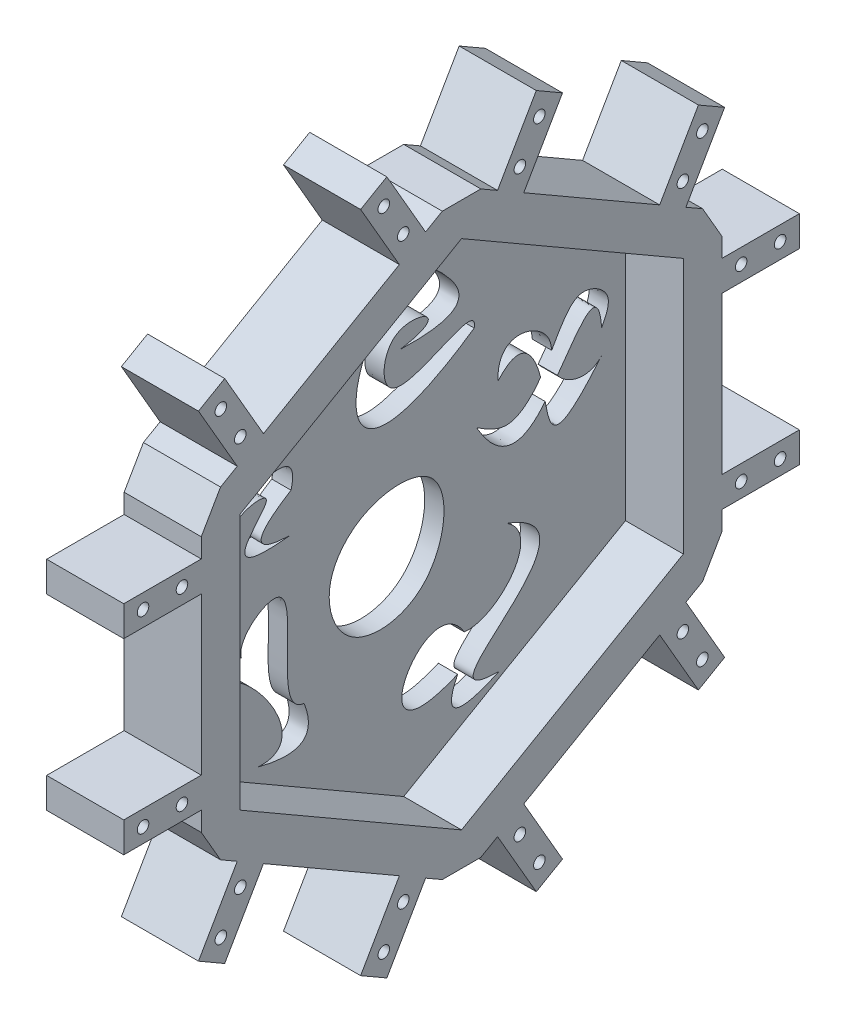
SolidWorks part; units mm, degrees
ref_plane "前视基准面" through (0, 0, 0) normal (0, 0, 1) x (1, 0, 0)
ref_plane "上视基准面" through (0, 0, 0) normal (0, 1, 0) x (1, 0, 0)
ref_plane "右视基准面" through (0, 0, 0) normal (1, 0, 0) x (0, 0, -1)
other "Configuration Table"
sketch "草图4" plane through (0, 0, 0) normal (1, 0, 0) x (0, 0, -1)
  line L0 (-57.5041, 33.2) -> (-57.5041, -23.2136)
  line L1 (-67.5041, -20.35) -> (-87.6041, -20.35)
  line L2 (-67.5041, 20.35) -> (-87.6041, 20.35)
  line L3 (-87.6041, 20.35) -> (-87.6041, 28.2)
  line L4 (-87.6041, 28.2) -> (-71.9735, 28.2)
  line L5 (-87.6041, -20.35) -> (-87.6041, -28.2)
  line L6 (-87.6041, -28.2) -> (-71.9735, -28.2)
  line L7 (-67.5041, 20.35) -> (-67.5041, -20.35)
  line L8 (-71.9735, 28.2) -> (-67.5041, 28.2)
  line L9 (-71.9735, -28.2) -> (-67.5041, -28.2)
  line L10 (-67.5041, 28.2) -> (-67.5041, 33.2)
  line L11 (0, 66.4) -> (-57.5041, 33.2) construction
  line L12 (-57.5041, 33.2) -> (-57.5041, -33.2) construction
  line L13 (-57.5041, -33.2) -> (0, -66.4) construction
  line L14 (0, -66.4) -> (57.5041, -33.2) construction
  line L15 (57.5041, -33.2) -> (57.5041, 33.2) construction
  line L16 (57.5041, 33.2) -> (0, 66.4) construction
  line L19 (-67.5041, -28.2) -> (-67.5041, -33.2)
  line L21 (-57.5041, -33.2) -> (-57.5041, -23.2136)
  line L22 (0, 66.4) -> (-48.8556, 38.1932)
  line L23 (-57.5041, 33.2) -> (-48.8556, 38.1932)
  line L25 (-58.174, 44.3603) -> (-62.5041, 41.8603)
  line L26 (-60.4087, 48.2309) -> (-58.174, 44.3603)
  line L27 (-68.224, 61.7674) -> (-60.4087, 48.2309)
  line L28 (-61.4257, 65.6924) -> (-68.224, 61.7674)
  line L29 (-51.3757, 48.2853) -> (-61.4257, 65.6924)
  line L30 (-16.1284, 68.6353) -> (-51.3757, 48.2853)
  line L31 (-16.1284, 68.6353) -> (-26.1784, 86.0424)
  line L32 (-26.1784, 86.0424) -> (-19.3801, 89.9674)
  line L33 (-19.3801, 89.9674) -> (-11.5648, 76.4309)
  line L34 (-11.5648, 76.4309) -> (-9.3301, 72.5603)
  line L35 (-9.3301, 72.5603) -> (-5, 75.0603)
  line L37 (57.5041, 33.2) -> (8.6484, 61.4068)
  line L38 (0, 66.4) -> (8.6484, 61.4068)
  line L40 (9.3301, 72.5603) -> (5, 75.0603)
  line L41 (11.5648, 76.4309) -> (9.3301, 72.5603)
  line L42 (19.3801, 89.9674) -> (11.5648, 76.4309)
  line L43 (26.1784, 86.0424) -> (19.3801, 89.9674)
  line L44 (16.1284, 68.6353) -> (26.1784, 86.0424)
  line L45 (51.3757, 48.2853) -> (16.1284, 68.6353)
  line L46 (51.3757, 48.2853) -> (61.4257, 65.6924)
  line L47 (61.4257, 65.6924) -> (68.224, 61.7674)
  line L48 (68.224, 61.7674) -> (60.4087, 48.2309)
  line L49 (60.4087, 48.2309) -> (58.174, 44.3603)
  line L50 (58.174, 44.3603) -> (62.5041, 41.8603)
  line L52 (57.5041, -33.2) -> (57.5041, 23.2136)
  line L53 (57.5041, 33.2) -> (57.5041, 23.2136)
  line L55 (67.5041, 28.2) -> (67.5041, 33.2)
  line L56 (71.9735, 28.2) -> (67.5041, 28.2)
  line L57 (87.6041, 28.2) -> (71.9735, 28.2)
  line L58 (87.6041, 20.35) -> (87.6041, 28.2)
  line L59 (67.5041, 20.35) -> (87.6041, 20.35)
  line L60 (67.5041, -20.35) -> (67.5041, 20.35)
  line L61 (67.5041, -20.35) -> (87.6041, -20.35)
  line L62 (87.6041, -20.35) -> (87.6041, -28.2)
  line L63 (87.6041, -28.2) -> (71.9735, -28.2)
  line L64 (71.9735, -28.2) -> (67.5041, -28.2)
  line L65 (67.5041, -28.2) -> (67.5041, -33.2)
  line L67 (0, -66.4) -> (48.8556, -38.1932)
  line L68 (57.5041, -33.2) -> (48.8556, -38.1932)
  line L70 (58.174, -44.3603) -> (62.5041, -41.8603)
  line L71 (60.4087, -48.2309) -> (58.174, -44.3603)
  line L72 (68.224, -61.7674) -> (60.4087, -48.2309)
  line L73 (61.4257, -65.6924) -> (68.224, -61.7674)
  line L74 (51.3757, -48.2853) -> (61.4257, -65.6924)
  line L75 (16.1284, -68.6353) -> (51.3757, -48.2853)
  line L76 (16.1284, -68.6353) -> (26.1784, -86.0424)
  line L77 (26.1784, -86.0424) -> (19.3801, -89.9674)
  line L78 (19.3801, -89.9674) -> (11.5648, -76.4309)
  line L79 (11.5648, -76.4309) -> (9.3301, -72.5603)
  line L80 (9.3301, -72.5603) -> (5, -75.0603)
  line L82 (-57.5041, -33.2) -> (-8.6484, -61.4068)
  line L83 (0, -66.4) -> (-8.6484, -61.4068)
  line L85 (-9.3301, -72.5603) -> (-5, -75.0603)
  line L86 (-11.5648, -76.4309) -> (-9.3301, -72.5603)
  line L87 (-19.3801, -89.9674) -> (-11.5648, -76.4309)
  line L88 (-26.1784, -86.0424) -> (-19.3801, -89.9674)
  line L89 (-16.1284, -68.6353) -> (-26.1784, -86.0424)
  line L90 (-51.3757, -48.2853) -> (-16.1284, -68.6353)
  line L91 (-51.3757, -48.2853) -> (-61.4257, -65.6924)
  line L92 (-61.4257, -65.6924) -> (-68.224, -61.7674)
  line L93 (-68.224, -61.7674) -> (-60.4087, -48.2309)
  line L94 (-60.4087, -48.2309) -> (-58.174, -44.3603)
  line L95 (-58.174, -44.3603) -> (-62.5041, -41.8603)
  line L97 (-62.5041, 41.8603) -> (-67.5041, 33.2)
  line L98 (-67.5041, -33.2) -> (-62.5041, -41.8603)
  line L99 (-5, -75.0603) -> (5, -75.0603)
  line L100 (62.5041, -41.8603) -> (67.5041, -33.2)
  line L101 (67.5041, 33.2) -> (62.5041, 41.8603)
  line L102 (-5, 75.0603) -> (5, 75.0603)
  circle A0 centre (-82.6041, 24.4) radius 1.5
  circle A1 centre (-72.5041, 24.4) radius 1.5
  circle A2 centre (-82.6041, -24.4) radius 1.5
  circle A3 centre (-72.5041, -24.4) radius 1.5
  circle A4 centre (0, 0) radius 57.5041 construction
  circle A5 centre (-15.121, 74.9904) radius 1.5
  circle A6 centre (-20.171, 83.7372) radius 1.5
  circle A7 centre (-62.4331, 59.3372) radius 1.5
  circle A8 centre (-57.3831, 50.5904) radius 1.5
  circle A9 centre (57.3831, 50.5904) radius 1.5
  circle A10 centre (62.4331, 59.3372) radius 1.5
  circle A11 centre (20.171, 83.7372) radius 1.5
  circle A12 centre (15.121, 74.9904) radius 1.5
  circle A13 centre (72.5041, -24.4) radius 1.5
  circle A14 centre (82.6041, -24.4) radius 1.5
  circle A15 centre (82.6041, 24.4) radius 1.5
  circle A16 centre (72.5041, 24.4) radius 1.5
  circle A17 centre (15.121, -74.9904) radius 1.5
  circle A18 centre (20.171, -83.7372) radius 1.5
  circle A19 centre (62.4331, -59.3372) radius 1.5
  circle A20 centre (57.3831, -50.5904) radius 1.5
  circle A21 centre (-57.3831, -50.5904) radius 1.5
  circle A22 centre (-62.4331, -59.3372) radius 1.5
  circle A23 centre (-20.171, -83.7372) radius 1.5
  circle A24 centre (-15.121, -74.9904) radius 1.5
  point P92 (0, 0)
  point P93 (0, 0)
  point P130 (0, 0)
  point P223 (0, 0)
  dimension "D1" = 5
  dimension "D2" = 5
  dimension "D3" = 66.4
  dimension "D4" = 66.4
  dimension "D5" = 6
extrude "凸台-拉伸2" add sketch "草图4" along normal blind 20 contours L83 L67 L68 L52 L53 L37 L38 L22 L23 L0 L21 L82 | L102 L35 L34 L33 L32 L31 L30 L29 L28 L27 L26 L25 L97 L10 L8 L4 L3 L2 L7 L1 L5 L6 L9 L19 L98 L95 L94 L93 L92 L91 L90 L89 L88 L87 L86 L85 L99 L80 L79 L78 L77 L76 L75 L74 L73 L72 L71 L70 L100 L65 L64
sketch "草图5" plane through (20, 0, 0) normal (1, 0, 0) x (0, 0, -1)
  line L0 (57.5041, 33.2) -> (57.5041, 23.2136) construction
  line L1 (57.5041, -33.2) -> (57.5041, 23.2136) construction
  line L2 (57.5041, -33.2) -> (48.8556, -38.1932) construction
  line L3 (0, -66.4) -> (48.8556, -38.1932) construction
  line L4 (0, -66.4) -> (-8.6484, -61.4068) construction
  line L5 (-57.5041, -33.2) -> (-8.6484, -61.4068) construction
  line L6 (-57.5041, -33.2) -> (-57.5041, -23.2136) construction
  line L7 (-57.5041, 33.2) -> (-57.5041, -23.2136) construction
  line L8 (0, 66.4) -> (8.6484, 61.4068) construction
  line L9 (57.5041, 33.2) -> (8.6484, 61.4068) construction
  line L10 (0, 66.4) -> (-48.8556, 38.1932) construction
  line L11 (-57.5041, 33.2) -> (-48.8556, 38.1932) construction
  line L12 (57.5041, 33.2) -> (57.5041, 23.2136)
  line L13 (57.5041, -33.2) -> (57.5041, 23.2136)
  line L14 (57.5041, -33.2) -> (48.8556, -38.1932)
  line L15 (0, -66.4) -> (48.8556, -38.1932)
  line L16 (0, -66.4) -> (-8.6484, -61.4068)
  line L17 (-57.5041, -33.2) -> (-8.6484, -61.4068)
  line L18 (-57.5041, -33.2) -> (-57.5041, -23.2136)
  line L19 (-57.5041, 33.2) -> (-57.5041, -23.2136)
  line L20 (0, 66.4) -> (8.6484, 61.4068)
  line L21 (57.5041, 33.2) -> (8.6484, 61.4068)
  line L22 (0, 66.4) -> (-48.8556, 38.1932)
  line L23 (-57.5041, 33.2) -> (-48.8556, 38.1932)
extrude "切除-拉伸3" cut sketch "草图5" against normal blind 15
sketch "草图7" plane through (5, 0, 0) normal (1, 0, 0) x (0, 0, -1)
  parabola Q7 (13.9762, -45.9372) -> (24.7114, -50.666) focus (13.626, -52.166) apex (12.9248, -52.7816)
  parabola Q8 (36.6699, 3.996) -> (18.8878, 6.9764) focus (28.4129, 1.7104) apex (28.3016, -1.2756)
  parabola Q9 (-25.8443, -32.5367) -> (-37.9619, -40.8605) focus (-26.9606, -39.1659) apex (-25.5772, -40.2492)
  parabola Q10 (-29.2292, 17.0148) -> (-29.6349, 6.9764) focus (-36.2224, 9.479) apex (-36.9122, 9.2751)
  parabola Q11 (-37.7904, 22.2656) -> (-29.2292, 17.0148) focus (-30.564, 21.4844) apex (-29.6349, 22.3646)
  parabola Q12 (-1.0238, 34.4585) -> (11.0222, 44.9602) focus (12.8063, 38.458) apex (14.1256, 37.9699)
  parabola Q13 (-43.1957, 34.3117) -> (-53.3885, 13.1539) focus (-37.4409, 32.769) apex (-36.6939, 33.194)
  spline S18 degree 3 poles (24.7114, -50.666) (-0.512, -50.303) (55.6609, -28.9266) (26.7802, -18.451) knots 0 0 0 0 1 1 1 1
  spline S19 degree 3 poles (15.6971, -37.2721) (5.8026, -21.0496) (-14.3001, -57.9644) (13.9762, -45.9372) knots 0 0 0 0 1 1 1 1
  spline S20 degree 3 poles (26.7802, -18.451) (36.5355, -24.7161) (24.136, -38.4634) (15.6971, -37.2721) knots 0 0 0 0 1 1 1 1
  spline S21 degree 3 poles (39.8546, 8.2668) (42.3529, 4.8779) (48.0849, 3.2843) (51.3195, 6.9764) knots 0.690631 0.690631 0.690631 0.690631 1 1 1 1
  spline S22 degree 3 poles (51.3195, 13.1539) (50.6112, 24.4163) (45.8101, 16.5845) (39.8546, 8.2668) knots 0 0 0 0 0.460407 0.460407 0.460407 0.460407
  spline S23 degree 3 poles (18.8878, 6.9764) (21.7996, 5.1473) (27.1015, 1.8168) (32.8839, 6.5569) (35.0024, 9.2622) (35.5003, 9.9606) knots 0 0 0 0 0.17996 0.327675 0.377932 0.377932 0.377932 0.377932
  spline S24 degree 3 poles (36.6699, 3.996) (37.9718, -3.4192) (39.2364, -7.7148) (51.3195, 6.9764) knots 0.489947 0.489947 0.489947 0.489947 1 1 1 1
  spline S25 degree 3 poles (24.4475, 14.6982) (23.9909, 25.9812) (37.2194, 22.4592) (38.2912, 15.4468) (38.3615, 14.6257) knots 0 0 0 0 0.465592 0.526149 0.526149 0.526149 0.526149
  spline S26 degree 3 poles (38.3615, 14.6257) (39.3478, 16.3802) (41.2457, 19.8021) (46.0468, 25.5335) (54.8958, 20.2046) (52.4248, 15.333) (51.3195, 13.1539) knots 0.486603 0.486603 0.486603 0.486603 0.606455 0.716129 0.873016 1 1 1 1
  spline S27 degree 3 poles (24.4475, 14.6982) (29.6924, 20.6396) (33.528, 16.6162) (35.2239, 11.0555) (35.5003, 9.9606) knots 0 0 0 0 0.29103 0.361024 0.361024 0.361024 0.361024
  spline S28 degree 3 poles (13.7217, 4.923) (-10.6736, 5.0862) (-22.1828, -9.0474) (-14.9969, -27.7307) (9.7069, -25.6568) (13.7217, 4.923) (-10.6736, 5.0862) (-22.1828, -9.0474) knots -0.65182 -0.447429 -0.18147 0 0.189535 0.34818 0.552571 0.81853 1 1.189535 1.34818 1.552571 only from (-8.894, 2.6928) to (-8.894, 2.6928)
  spline S29 degree 3 poles (-49.0854, -23.9429) (-51.2191, -3.3676) (-17.9582, -42.2672) (-37.9619, -40.8605) knots 0 0 0 0 1 1 1 1
  spline S30 degree 3 poles (-49.0854, -23.9429) (-58.5196, -17.6143) (-47.2215, -10.8473) (-42.1072, -14.2686) knots 0 0 0 0 1 1 1 1
  spline S31 degree 3 poles (-42.1072, -14.2686) (-43.37, -9.821) (-22.1192, 5.9611) (-34.5803, -31.7225) (-25.8443, -32.5367) knots 0 0 0 0 0.32815 1 1 1 1
  spline S32 degree 3 poles (-53.3885, 13.1539) (-48.6647, 6.3828) (-47.5793, 18.7317) (-28.1001, 19.6759) (-51.9094, 4.4709) (-29.6349, 6.9764) knots 0 0 0 0 0.436573 0.602263 1 1 1 1
  spline S33 degree 3 poles (-43.1957, 34.3117) (-42.3709, 39.9811) (-18.4721, 38.9182) (-37.6204, 23.2016) (-37.7904, 22.2656) knots 0 0 0 0 0.500983 1 1 1 1
  spline S34 degree 3 poles (11.0222, 44.9602) (-7.1549, 68.0095) (-34.2637, -6.4332) (18.2808, 29.671) knots 0 0 0 0 1 1 1 1
  spline S35 degree 3 poles (-1.0238, 34.4585) (13.6498, 36.7571) (-4.9092, 45.0796) (-6.9816, 16.0199) (19.5794, 36.9409) (18.2808, 29.671) knots 0 0 0 0 0.322419 0.551081 1 1 1 1
  point P0 (44.0609, 5.2776)
  point P2 (33.8681, 7.903)
  point P4 (14.2654, 39.5549)
extrude "切除-拉伸7" cut sketch "草图7" against normal up to next
